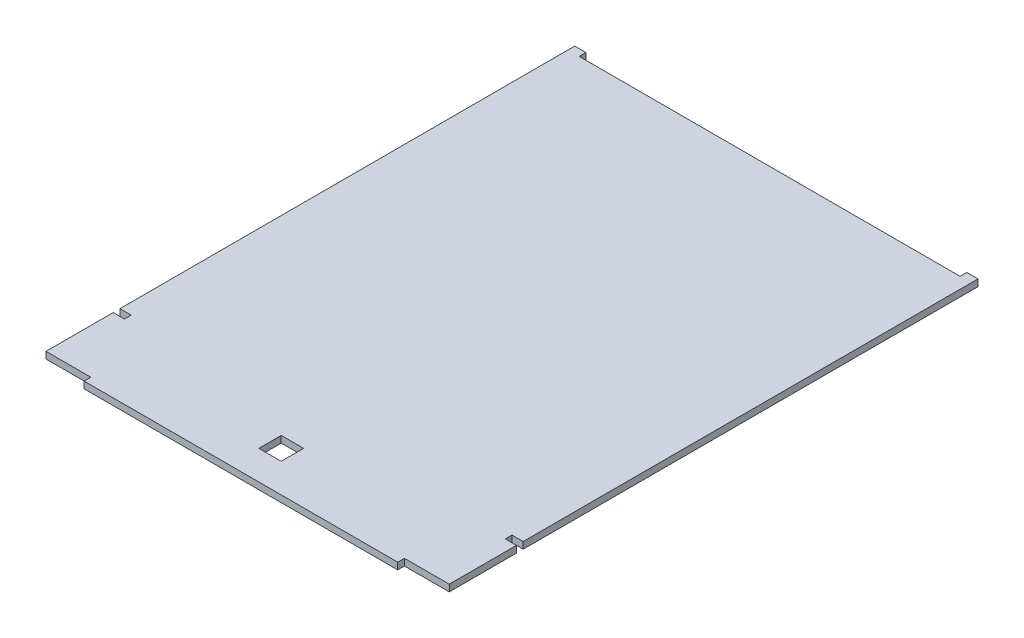
SolidWorks part; units mm, degrees
ref_plane "前视基准面" through (0, 0, 0) normal (0, 0, 1) x (1, 0, 0)
ref_plane "上视基准面" through (0, 0, 0) normal (0, 1, 0) x (1, 0, 0)
ref_plane "右视基准面" through (0, 0, 0) normal (1, 0, 0) x (0, 0, -1)
sketch "草图1" plane through (0, 0, 0) normal (0, 1, 0) x (1, 0, 0)
  line L2 (0, 0) -> (0, 27)
  line L3 (0, 30) -> (5, 30)
  line L4 (180, 0) -> (180, 27)
  line L5 (0, 30) -> (5, 30)
  line L6 (0, 30) -> (0, 230)
  line L7 (5, 230) -> (175, 230)
  line L8 (180, 30) -> (180, 230)
  line L10 (85, 7) -> (95, 7)
  line L11 (95, 7) -> (95, 17)
  line L12 (95, 17) -> (85, 17)
  line L13 (0, 30) -> (5, 30)
  line L14 (5, 30) -> (5, 27)
  line L15 (5, 27) -> (0, 27)
  line L16 (180, 30) -> (175, 30)
  line L17 (175, 30) -> (175, 27)
  line L18 (175, 27) -> (180, 27)
  line L19 (175, 30) -> (180, 30)
  line L20 (175, 30) -> (180, 30)
  line L21 (0, 230) -> (0, 233)
  line L22 (0, 233) -> (5, 233)
  line L23 (5, 233) -> (5, 230)
  line L25 (175, 230) -> (175, 233)
  line L26 (175, 233) -> (180, 233)
  line L27 (180, 233) -> (180, 230)
  line L28 (85, 17) -> (85, 7)
  line L29 (0, 0) -> (0, -3)
  line L30 (0, -3) -> (20, -3)
  line L31 (20, -3) -> (20, -6)
  line L32 (20, -6) -> (160, -6)
  line L33 (160, -6) -> (160, -3)
  line L34 (160, -3) -> (180, -3)
  line L35 (180, -3) -> (180, 0)
  point P31 (90, 7)
extrude "凸台-拉伸1" add sketch "草图1" along normal blind 3 contours L34 L35 L4 L18 L17 L16 L8 L27 L26 L25 L7 L23 L22 L21 L6 L3 L14 L15 L2 L29 L30 L31 L32 L33 L28 L12 L11 L10
